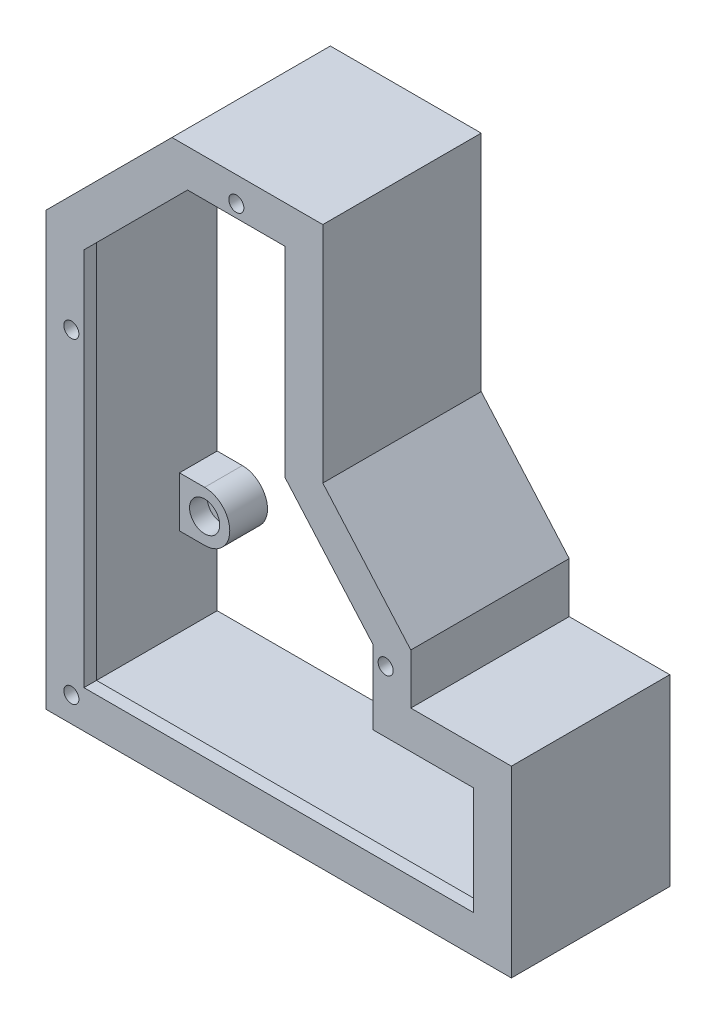
SolidWorks part; units mm, degrees
ref_plane "前视基准面" through (0, 0, 0) normal (0, 0, 1) x (1, 0, 0)
ref_plane "上视基准面" through (0, 0, 0) normal (0, 1, 0) x (1, 0, 0)
ref_plane "右视基准面" through (0, 0, 0) normal (1, 0, 0) x (0, 0, -1)
sketch "草图1" plane through (0, 0, 0) normal (0, 0, 1) x (1, 0, 0)
  line L0 (100, -2.0318) -> (60, -2.0318)
  line L1 (60, -2.0318) -> (60, 17.9682)
  line L2 (60, 17.9682) -> (25, 57.9682)
  line L3 (25, 57.9682) -> (25, 147)
  line L14 (-85, -80) -> (100, -80)
  line L15 (100, -80) -> (100, -2.0318)
  line L18 (25, 147) -> (-35, 147)
  line L19 (-35, 147) -> (-85, 97)
  line L20 (-85, 97) -> (-85, -80)
  dimension "D1" = 60
  dimension "D2" = 40
  dimension "D3" = 185
  dimension "D4" = 227
  dimension "D5" = 35
  dimension "D6" = 40
  dimension "D7" = 20
extrude "凸台-拉伸1" add sketch "草图1" along normal blind 63
sketch "草图2" plane through (0, 0, 63) normal (0, 0, 1) x (1, 0, 0)
  line L0 (100, -80) -> (100, -2.0318) construction
  line L1 (-85, -80) -> (100, -80)
  line L2 (-85, -80) -> (-85, -75)
  line L3 (-85, -75) -> (100, -75)
  line L4 (100, -80) -> (100, -75)
  dimension "D1" = 5
extrude "切除-拉伸1" cut sketch "草图2" against normal blind 114
shell "抽壳1" thickness 5
sketch "草图3" plane through (0, 0, 58) normal (0, 0, -1) x (-1, 0, 0)
  line L18 (-85, -60) -> (70, -60)
  line L19 (70, -60) -> (70, 90.7868)
  line L20 (70, 90.7868) -> (28.7868, 132)
  line L21 (28.7868, 132) -> (-10, 132)
  line L22 (-10, 132) -> (-10, 52.3322)
  line L23 (-10, 52.3322) -> (-45, 12.3322)
  line L24 (-45, 12.3322) -> (-45, -17.0318)
  line L25 (-45, -17.0318) -> (-85, -17.0318)
  line L26 (-85, -17.0318) -> (-85, -60)
  line L27 (-85, -60) -> (70, -60)
  line L28 (70, -60) -> (70, 90.7868)
  line L29 (70, 90.7868) -> (28.7868, 132)
  line L30 (28.7868, 132) -> (-10, 132)
  line L31 (-10, 132) -> (-10, 52.3322)
  line L32 (-10, 52.3322) -> (-45, 12.3322)
  line L33 (-45, 12.3322) -> (-45, -17.0318)
  line L34 (-45, -17.0318) -> (-85, -17.0318)
  line L35 (-85, -17.0318) -> (-85, -60)
  dimension "D1" = 10
extrude "切除-拉伸2" cut sketch "草图3" against normal blind 10
sketch "草图4" plane through (0, 0, 0) normal (0, 0, -1) x (-1, 0, 0)
  line L0 (-20, 142) -> (32.9289, 142) construction
  line L2 (-10, 132) -> (-10, 52.3322) construction
  line L3 (70, 90.7868) -> (28.7868, 132) construction
  line L4 (70, -60) -> (70, 90.7868) construction
  line L5 (-85, -60) -> (70, -60) construction
  line L6 (-100, -75) -> (85, -75) construction
  line L7 (-100, -75) -> (-100, -2.0318) construction
  line L8 (63.5355, 111.3934) -> (56.4645, 104.3223)
  line L9 (32.9289, 142) -> (80, 94.9289) construction
  line L10 (63.5355, 111.3934) -> (49.3934, 125.5355)
  line L11 (49.3934, 125.5355) -> (42.3223, 118.4645)
  line L12 (70, -15) -> (80, -15)
  line L13 (80, 94.9289) -> (80, -70) construction
  line L14 (80, -15) -> (80, -35)
  line L15 (80, -35) -> (70, -35)
  line L16 (-40, -60) -> (-40, -70)
  line L17 (-95, -70) -> (80, -70) construction
  line L18 (-40, -70) -> (-60, -70)
  line L19 (-60, -70) -> (-60, -60)
  line L20 (-10, 127) -> (-20, 127)
  line L21 (-20, 56.0895) -> (-20, 142) construction
  line L22 (-20, 127) -> (-20, 107)
  line L23 (-20, 107) -> (-10, 107)
  arc A0 (70, -15) -> (70, -35) centre (70, -25) ccw
  arc A1 (-40, -60) -> (-60, -60) centre (-50, -60) ccw
  arc A2 (-10, 107) -> (-10, 127) centre (-10, 117) ccw
  arc A3 (42.3223, 118.4645) -> (56.4645, 104.3223) centre (49.3934, 111.3934) ccw
  dimension "D1" = 20
  dimension "D2" = 20
  dimension "D3" = 20
  dimension "D4" = 20
  dimension "D5" = 50
  dimension "D6" = 50
  dimension "D7" = 25
extrude "凸台-拉伸2" add sketch "草图4" against normal blind 15
sketch "草图5" plane through (0, 0, 0) normal (0, 0, -1) x (-1, 0, 0)
  circle A0 centre (49.3934, 111.3934) radius 3
  circle A1 centre (-10, 117) radius 3
  circle A2 centre (70, -25) radius 3
  circle A3 centre (-50, -60) radius 3
  dimension "D1" = 6
  dimension "D2" = 6
  dimension "D3" = 6
  dimension "D4" = 6
extrude "切除-拉伸3" cut sketch "草图5" against normal blind 35
sketch "草图6" plane through (0, 0, 15) normal (0, 0, 1) x (1, 0, 0)
  line L0 (-28.7868, 132) -> (-70, 90.7868) construction
  circle A0 centre (10, 117) radius 6
  circle A1 centre (-49.3934, 111.3934) radius 6
  circle A2 centre (50, -60) radius 6
  circle A3 centre (-70, -25) radius 6
  dimension "D1" = 12
  dimension "D2" = 12
  dimension "D3" = 12
  dimension "D4" = 12
extrude "切除-拉伸4" cut sketch "草图6" against normal blind 7
sketch "草图8" plane through (0, 0, 63) normal (0, 0, 1) x (1, 0, 0)
  line L0 (10, 132) -> (-28.7868, 132) construction
  line L1 (45, -17.0318) -> (45, 12.3322) construction
  line L2 (95, -70) -> (-80, -70) construction
  line L3 (-80, 94.9289) -> (-80, -70) construction
  line L4 (-70, 90.7868) -> (-70, -60) construction
  circle A0 centre (-9.3934, 137) radius 3
  circle A1 centre (-75, -65) radius 3
  circle A2 centre (-75, 60.7868) radius 3
  circle A3 centre (50, 7.3322) radius 3
  dimension "D1" = 6
  dimension "D2" = 5
  dimension "D3" = 6
  dimension "D4" = 5
  dimension "D5" = 5
  dimension "D6" = 6
  dimension "D7" = 5
  dimension "D8" = 5
  dimension "D9" = 6
  dimension "D10" = 5
  dimension "D11" = 30
extrude "切除-拉伸5" cut sketch "草图8" against normal blind 10
